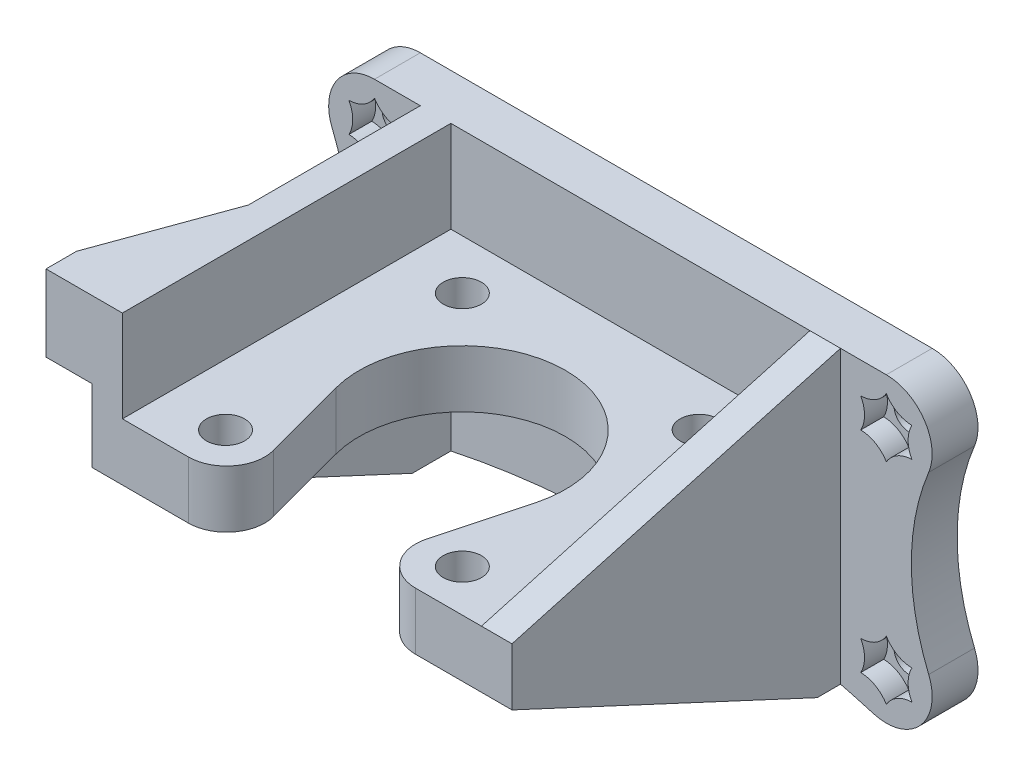
SolidWorks part; units mm, degrees
ref_plane "Front Plane" through (0, 0, 0) normal (0, 0, 1) x (1, 0, 0)
ref_plane "Top Plane" through (0, 0, 0) normal (0, 1, 0) x (1, 0, 0)
ref_plane "Right Plane" through (0, 0, 0) normal (1, 0, 0) x (0, 0, -1)
sketch "Sketch1" plane through (0, 0, 0) normal (0, 0, 1) x (1, 0, 0)
  line L0 (4, 7.5) -> (4, 19.5)
  line L5 (0, 0) -> (55, 0)
  line L7 (4, 7.5) -> (55, 7.5)
  line L8 (55, 0) -> (55, 7.5)
  line L9 (0, 19.5) -> (4, 19.5)
  line L12 (0, 19.5) -> (0, 0)
  dimension "D1" = 51
  dimension "D2" = 12
  dimension "D3" = 4
  dimension "D6" = 7.5
extrude "Boss-Extrude1" add sketch "Sketch1" along normal blind 49
sketch "Sketch2" plane through (0, 7.5, 0) normal (0, 1, 0) x (1, 0, 0)
  line L0 (55, -49) -> (4, -49) construction
  line L1 (55, -49) -> (55, 0) construction
  line L2 (43, -12.5) -> (12, -43.5) construction
  line L3 (14.46, -31.4941) -> (19.1507, -49)
  line L4 (19.1507, -49) -> (35.8493, -49)
  line L5 (35.8493, -49) -> (40.54, -31.4941)
  line L6 (27.5, -28) -> (27.5, -40.6945) construction
  arc A0 (40.54, -31.4941) -> (14.46, -31.4941) centre (27.5, -28) ccw
  circle A1 centre (12, -12.5) radius 2.5
  circle A2 centre (43, -12.5) radius 2.5
  circle A3 centre (12, -43.5) radius 2.5
  circle A4 centre (43, -43.5) radius 2.5
  dimension "D3" = 27
  dimension "D6" = 5
  dimension "D1" = 21
  dimension "D2" = 27.5
  dimension "D4" = 31
  dimension "D5" = 31
  dimension "D7" = 15
  dimension "D8" = 15
extrude "Cut-Extrude1" cut sketch "Sketch2" against normal through all
sketch "Sketch4" plane through (0, 0, 0) normal (0, 0, -1) x (-1, 0, 0)
  line L1 (12, -20) -> (-67, -20)
  line L2 (12, -20) -> (12, 19.5)
  line L3 (12, 19.5) -> (-67, 19.5)
  line L4 (-67, -20) -> (-67, 19.5)
  line L5 (-4, 19.5) -> (0, 19.5) construction
  line L6 (0, 19.5) -> (0, 0) construction
  line L8 (-55, 0) -> (-55, 7.5) construction
  line L9 (0, 0) -> (-55, 0) construction
  dimension "D1" = 12
  dimension "D2" = 20
  dimension "D3" = 12
extrude "Boss-Extrude2" add sketch "Sketch4" against normal blind 6
sketch "Sketch6" plane through (0, 0, 0) normal (-1, 0, 0) x (0, 0, 1)
  line L0 (6, -20) -> (49, 0)
  line L1 (49, 0) -> (6, 0)
  line L2 (6, 0) -> (6, -20)
  line L4 (49, 19.5) -> (49, 0) construction
extrude "Boss-Extrude3" add sketch "Sketch6" against normal up to surface (4 mm away) up to face at (4, 13.5, 27.5)
sketch "Sketch5" plane through (0, 0, 0) normal (0, 0, -1) x (-1, 0, 0)
  line L1 (12, -20) -> (12, 19.5) construction
  line L4 (-67, -20) -> (12, -20) construction
  line L5 (-67, 19.5) -> (12, 19.5) construction
  line L6 (-67, 19.5) -> (-67, -20) construction
  circle A0 centre (-61, 13.5) radius 2
  circle A1 centre (-61, -14) radius 2
  circle A2 centre (6, 13.5) radius 2
  circle A3 centre (6, -14) radius 2
  dimension "D5" = 4
  dimension "D1" = 6
  dimension "D2" = 6
  dimension "D3" = 6
  dimension "D4" = 6
extrude "Cut-Extrude3" cut sketch "Sketch5" against normal blind 10
sketch "Sketch7" plane through (55, 0, 0) normal (1, 0, 0) x (0, 0, -1)
  line L0 (-49, 7.5) -> (-6, 19.5)
  line L1 (-6, 19.5) -> (0, 19.5)
  line L2 (0, 19.5) -> (0, -20)
  line L3 (0, -20) -> (-6, -20)
  line L4 (-6, -20) -> (-49, 0)
  line L5 (-49, 0) -> (-49, 7.5)
  line L6 (-6, 19.5) -> (-6, -20) construction
  line L7 (-6, 19.5) -> (0, 19.5) construction
  line L8 (-6, -20) -> (0, -20) construction
  line L9 (0, 19.5) -> (0, -20) construction
extrude "Boss-Extrude4" add sketch "Sketch7" against normal blind 4
fillet "Fillet1" radius 6 4 edges at (67, 19.5, 3) (67, -20, 3) (-12, -20, 3) (-12, 19.5, 3)
fillet "Fillet2" radius 5 2 edges at (35.8493, 3.75, 49) (19.1507, 3.75, 49)
sketch "Sketch9" plane through (0, 0, 6) normal (0, 0, 1) x (1, 0, 0)
  line L1 (-6, 16.7909) -> (-8.85, 15.1454)
  line L2 (-8.85, 15.1454) -> (-8.85, 11.8546)
  line L3 (-8.85, 11.8546) -> (-6, 10.2091)
  line L4 (-6, 10.2091) -> (-3.15, 11.8546)
  line L5 (-3.15, 11.8546) -> (-3.15, 15.1454)
  line L6 (-3.15, 15.1454) -> (-6, 16.7909)
  line L7 (-6, -10.7091) -> (-8.85, -12.3546)
  line L8 (-8.85, -12.3546) -> (-8.85, -15.6454)
  line L9 (-8.85, -15.6454) -> (-6, -17.2909)
  line L10 (-6, -17.2909) -> (-3.15, -15.6454)
  line L11 (-3.15, -15.6454) -> (-3.15, -12.3546)
  line L12 (-3.15, -12.3546) -> (-6, -10.7091)
  line L13 (61, -10.7091) -> (58.15, -12.3546)
  line L14 (58.15, -12.3546) -> (58.15, -15.6454)
  line L15 (58.15, -15.6454) -> (61, -17.2909)
  line L16 (61, -17.2909) -> (63.85, -15.6454)
  line L17 (63.85, -15.6454) -> (63.85, -12.3546)
  line L18 (63.85, -12.3546) -> (61, -10.7091)
  line L19 (61, 10.2091) -> (63.85, 11.8546)
  line L20 (63.85, 11.8546) -> (63.85, 15.1454)
  line L21 (63.85, 15.1454) -> (61, 16.7909)
  line L22 (61, 16.7909) -> (58.15, 15.1454)
  line L23 (58.15, 15.1454) -> (58.15, 11.8546)
  line L24 (58.15, 11.8546) -> (61, 10.2091)
  circle A0 centre (-6, 13.5) radius 2.85 construction
  circle A1 centre (-6, -14) radius 2.85 construction
  circle A2 centre (61, -14) radius 2.85 construction
  circle A3 centre (61, 13.5) radius 2.85 construction
  dimension "D1" = 5.7
extrude "Cut-Extrude5" cut sketch "Sketch9" against normal blind 3
sketch "Sketch10" plane through (0, 0, 0) normal (0, 0, -1) x (-1, 0, 0)
  line L0 (-61, 19.5) -> (-61, 26.1947)
  line L1 (-61, 26.1947) -> (-93.2137, 26.1947)
  line L2 (-93.2137, 26.1947) -> (-93.2137, -32.4835)
  line L3 (-93.2137, -32.4835) -> (20.6568, -32.4835)
  line L4 (20.6568, -32.4835) -> (20.6568, 27.2405)
  line L5 (20.6568, 27.2405) -> (6, 27.2405)
  line L6 (6, 27.2405) -> (6, 19.5)
  arc A0 (-61, 19.5) -> (-67, 13.5) centre (-61, 13.5) ccw construction
  arc A1 (-67, -14) -> (-61, -20) centre (-61, -14) ccw construction
  arc A2 (6, -20) -> (12, -14) centre (6, -14) ccw construction
  arc A3 (12, 13.5) -> (6, 19.5) centre (6, 13.5) ccw construction
  arc A4 (-61, 19.5) -> (-66.5451, 11.2083) centre (-61, 13.5) ccw
  arc A5 (-66.5451, -11.7083) -> (-59.3038, -19.7552) centre (-61, -14) ccw
  arc A6 (4.3038, -19.7552) -> (11.5451, -11.7083) centre (6, -14) ccw
  arc A7 (11.5451, 11.2083) -> (6, 19.5) centre (6, 13.5) ccw
  arc A8 (-66.5451, -11.7083) -> (-66.5451, 11.2083) centre (-94.2707, -0.25) ccw
  arc A9 (11.5451, 11.2083) -> (11.5451, -11.7083) centre (39.2707, -0.25) ccw
  arc A10 (4.3038, -19.7552) -> (-59.3038, -19.7552) centre (-27.5, -127.6662) ccw
  dimension "D1" = 30
  dimension "D2" = 112.5
extrude "Cut-Extrude6" cut sketch "Sketch10" against normal through all
sketch "Sketch11" plane through (0, 0, 6) normal (0, 0, 1) x (1, 0, 0)
  line L0 (-6, 16.7909) -> (-8.85, 15.1454) construction
  line L1 (-6, 17.3682) -> (-9.35, 15.4341) construction
  line L2 (-9.35, 15.4341) -> (-9.35, 11.5659) construction
  line L3 (-9.35, 11.5659) -> (-6, 9.6318) construction
  line L4 (-6, 9.6318) -> (-2.65, 11.5659) construction
  line L5 (-2.65, 11.5659) -> (-2.65, 15.4341) construction
  line L6 (-2.65, 15.4341) -> (-6, 17.3682) construction
  line L7 (-8.85, 15.1454) -> (-8.85, 11.8546) construction
  line L8 (-8.85, 11.8546) -> (-6, 10.2091) construction
  line L9 (-6, 10.2091) -> (-3.15, 11.8546) construction
  line L10 (-3.15, 11.8546) -> (-3.15, 15.1454) construction
  line L11 (-3.15, 15.1454) -> (-6, 16.7909) construction
  circle A0 centre (-6, 13.5) radius 3.35 construction
  arc A1 (-9.35, 15.4341) -> (-9.35, 11.5659) centre (-12.8408, 13.5) cw
  arc A2 (-9.35, 11.5659) -> (-6, 9.6318) centre (-9.4204, 7.5757) cw
  arc A3 (-6, 9.6318) -> (-2.65, 11.5659) centre (-2.5796, 7.5757) cw
  arc A4 (-2.65, 11.5659) -> (-2.65, 15.4341) centre (0.8408, 13.5) cw
  arc A5 (-6, 17.3682) -> (-2.65, 15.4341) centre (-2.5796, 19.4243) ccw
  arc A6 (-6, 17.3682) -> (-9.35, 15.4341) centre (-9.4204, 19.4243) cw
  dimension "D1" = 6.7
extrude "Cut-Extrude7" cut sketch "Sketch11" against normal up to surface (3 mm away) up to face at (-6, 13.5, 3)
pattern_linear "LPattern1" count 2 spacing 67 along (1, 0, 0) count 2 spacing 27.5 along (0, -1, 0) of "Cut-Extrude7"
sketch "Sketch12" plane through (0, 19.5, 0) normal (0, 1, 0) x (1, 0, 0)
  line L0 (0, -49) -> (-6, -49)
  line L1 (-6, -49) -> (-6, -45)
  line L2 (-6, -45) -> (0, -28.5151)
  line L3 (0, -49) -> (0, -6) construction
  line L4 (0, -28.5151) -> (0, -49)
  dimension "D1" = 6
  dimension "D2" = 4
  dimension "D3" = 20
extrude "Boss-Extrude5" add sketch "Sketch12" against normal blind 10
